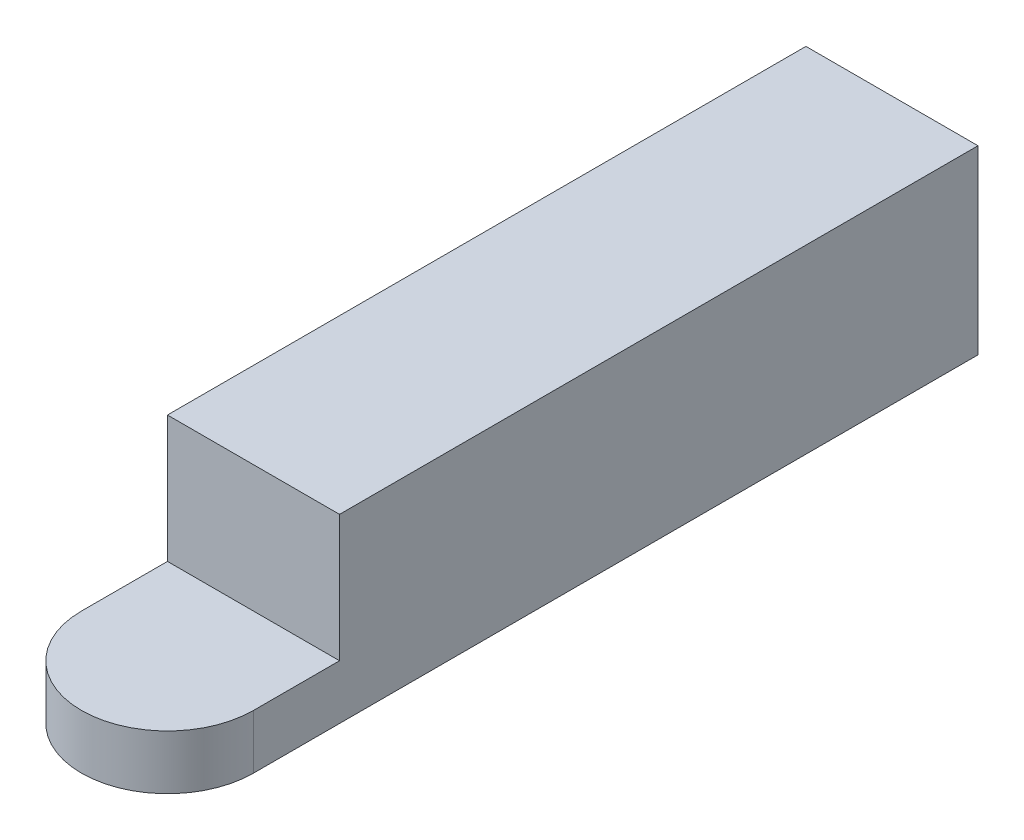
SolidWorks part; units mm, degrees
material "ABS"
ref_plane "Front Plane" through (0, 0, 0) normal (0, 0, 1) x (1, 0, 0)
ref_plane "Top Plane" through (0, 0, 0) normal (0, 1, 0) x (1, 0, 0)
ref_plane "Right Plane" through (0, 0, 0) normal (1, 0, 0) x (0, 0, -1)
sketch "Sketch1" plane through (0, 0, 0) normal (0, 1, 0) x (1, 0, 0)
  circle A0 centre (0, 0) radius 4.75
  dimension "D1" = 9.5
extrude "Boss-Extrude1" add sketch "Sketch1" along normal blind 3
sketch "Sketch2" plane through (0, 0, 0) normal (0, 1, 0) x (1, 0, 0)
  line L0 (-4.75, 0) -> (-4.75, 40)
  line L1 (4.75, 0) -> (4.75, 40)
  line L2 (4.75, 40) -> (-4.75, 40)
  circle A0 centre (0, 0) radius 4.75 construction
  arc A1 (4.75, 0) -> (-4.75, 0) centre (0, 0) ccw
  point P6 (0, 0)
  dimension "D1" = 40
extrude "Boss-Extrude2" add sketch "Sketch2" along normal blind 10
sketch "Sketch3" plane through (0, 10, 0) normal (0, 1, 0) x (1, 0, 0)
  line L0 (0, 4.75) -> (-4.75, 4.75)
  line L1 (-4.75, 40) -> (-4.75, 0) construction
  line L2 (0, 4.75) -> (4.75, 4.75)
  line L3 (4.75, 0) -> (4.75, 40) construction
  line L4 (4.75, 4.75) -> (4.75, 0)
  line L5 (-4.75, 4.75) -> (-4.75, 0)
  arc A0 (4.75, 0) -> (-4.75, 0) centre (0, 0) ccw construction
  arc A1 (4.75, 0) -> (-4.75, 0) centre (0, 0) ccw
  arc M1 (-4.75, 0) -> (4.75, 0) centre (0, 0) cw
  line M2 (4.75, 0) -> (4.75, 40)
  line M4 (-4.75, 40) -> (-4.75, 0)
extrude "Cut-Extrude1" cut sketch "Sketch3" against normal blind 7 contours L0 M1 M4 | L2 M1 M2
